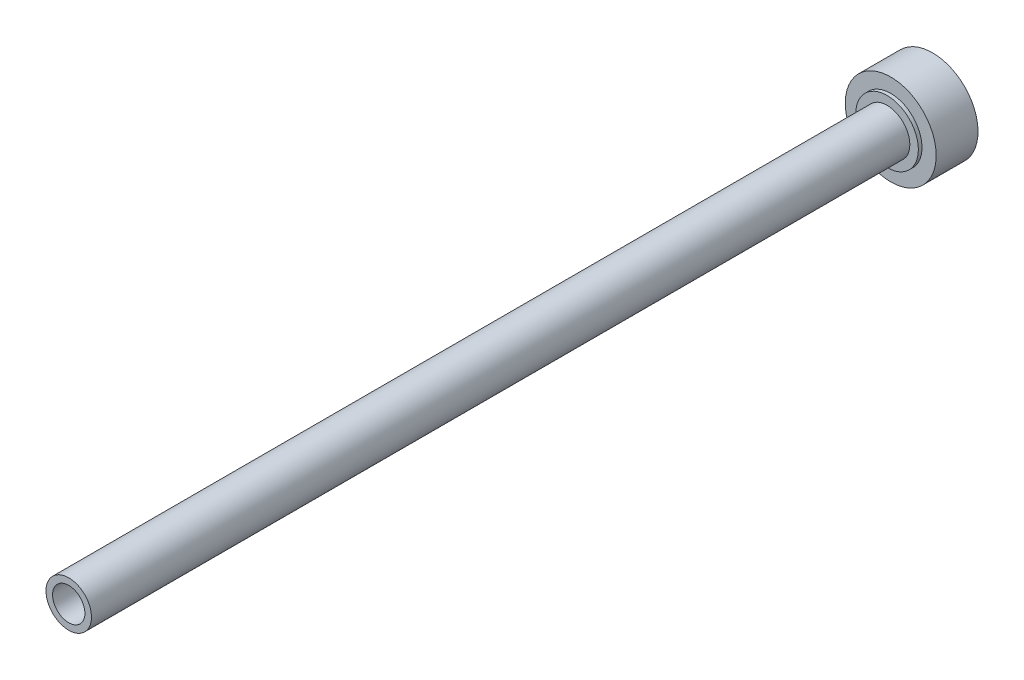
SolidWorks part; units mm, degrees
material "201 Annealed Stainless Steel (SS)"
ref_plane "Front Plane" through (0, 0, 0) normal (0, 0, 1) x (1, 0, 0)
ref_plane "Top Plane" through (0, 0, 0) normal (0, 1, 0) x (1, 0, 0)
ref_plane "Right Plane" through (0, 0, 0) normal (1, 0, 0) x (0, 0, -1)
sketch "Sketch1" plane through (0, 0, 0) normal (1, 0, 0) x (0, 0, -1)
  line L0 (-28.575, 0) -> (28.575, 0)
  line L1 (28.575, 0) -> (28.575, 1.5875)
  line L2 (28.575, 1.5875) -> (-28.575, 1.5875)
  line L3 (-28.575, 1.5875) -> (-28.575, 0)
  line L4 (28.575, 0) -> (-28.575, 0) construction
  line L5 (28.575, 1.5875) -> (28.575, 2.1828)
  line L6 (28.575, 2.1828) -> (28.829, 2.1828)
  line L7 (28.829, 2.1828) -> (28.829, 3.175)
  line L8 (28.829, 3.175) -> (31.75, 3.175)
  line L9 (31.75, 3.175) -> (31.75, 0)
  line L10 (31.75, 0) -> (28.575, 0)
  line L11 (28.575, 1.5875) -> (28.575, 2.1828)
  point P4 (0, 0)
  dimension "D1" = 1.5875
  dimension "D2" = 57.15
  dimension "D3" = 2.1828
  dimension "D4" = 0.254
  dimension "D5" = 3.175
  dimension "D6" = 3.175
revolve "Revolve1" add sketch "Sketch1" angle 360 about L0
hole_wizard "#4-40 Tapped Hole1" positions "Sketch2" profile "Sketch4" tap size "#4-40" standard "ANSI Inch"
sketch "Sketch2" plane through (0, 0, 28.575) normal (0, 0, 1) x (1, 0, 0)
  point P0 (0, 0)
sketch "Sketch4" plane through (0, 0, 28.575) normal (1, 0, 0) x (0, -1, 0)
  line L0 (0, 0) -> (0, 8.2992)
  line L1 (0, 8.2992) -> (1.1303, 7.62)
  line L2 (1.1303, 7.62) -> (1.1303, 0)
  line L5 (1.1303, 0) -> (0, 0)
  line L10 (0, 8.2992) -> (-1.1303, 7.62) construction
  line L11 (0, -6.35) -> (0, 107.95) construction
  dimension "Tap Drill Dia." = 2.2606
  dimension "Tap Drill Depth" = 7.62
  dimension "Drill Angle" = 118
cosmetic thread "Hole Thread1" parameters "D1"=5.588, "D2"=2.8448
